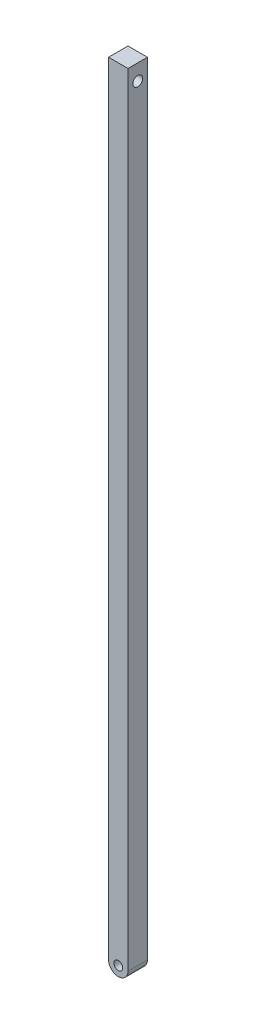
SolidWorks part; units mm, degrees
material "Galvanized Steel"
ref_plane "Front Plane" through (0, 0, 0) normal (0, 0, 1) x (1, 0, 0)
ref_plane "Top Plane" through (0, 0, 0) normal (0, 1, 0) x (1, 0, 0)
ref_plane "Right Plane" through (0, 0, 0) normal (1, 0, 0) x (0, 0, -1)
sketch "Sketch1" plane through (0, 0, 0) normal (0, 0, 1) x (1, 0, 0)
  line L0 (3.4438, -27.3561) -> (3.4438, -66.7561)
  line L1 (4.4438, -27.3561) -> (4.4438, -66.7561)
  line L2 (3.4438, -27.3561) -> (3.4438, -26.5411)
  line L3 (3.4438, -26.5411) -> (4.4438, -26.5411)
  line L4 (4.4438, -26.5411) -> (4.4438, -27.3561)
  line L5 (3.4438, -27.3561) -> (4.4438, -27.3561) construction
  arc A0 (3.4438, -66.7561) -> (4.4438, -66.7561) centre (3.9438, -66.7561) ccw
  circle A1 centre (3.9438, -66.7561) radius 0.2278
  dimension "D1" = 39.4
  dimension "D2" = 1
extrude "Boss-Extrude1" add sketch "Sketch1" along normal blind 1
sketch "Sketch3" plane through (0, 0, 1) normal (0, 0, 1) x (1, 0, 0)
  line L0 (3.9438, -66.7561) -> (3.9438, -27.3561) construction
  line L1 (3.9438, -27.3561) -> (4.4438, -27.3561) construction
  line L2 (4.4438, -66.7561) -> (4.4438, -26.5411) construction
  dimension "D1" = 39.4
sketch "Sketch4" plane through (4.4438, 0, 0) normal (1, 0, 0) x (0, 0, -1)
  line L0 (-1, -27.3561) -> (0, -27.3561) construction
  line L1 (0, -66.7561) -> (0, -26.5411) construction
  circle A0 centre (-0.5, -27.3561) radius 0.252
extrude "Cut-Extrude1" cut sketch "Sketch4" against normal blind 10
